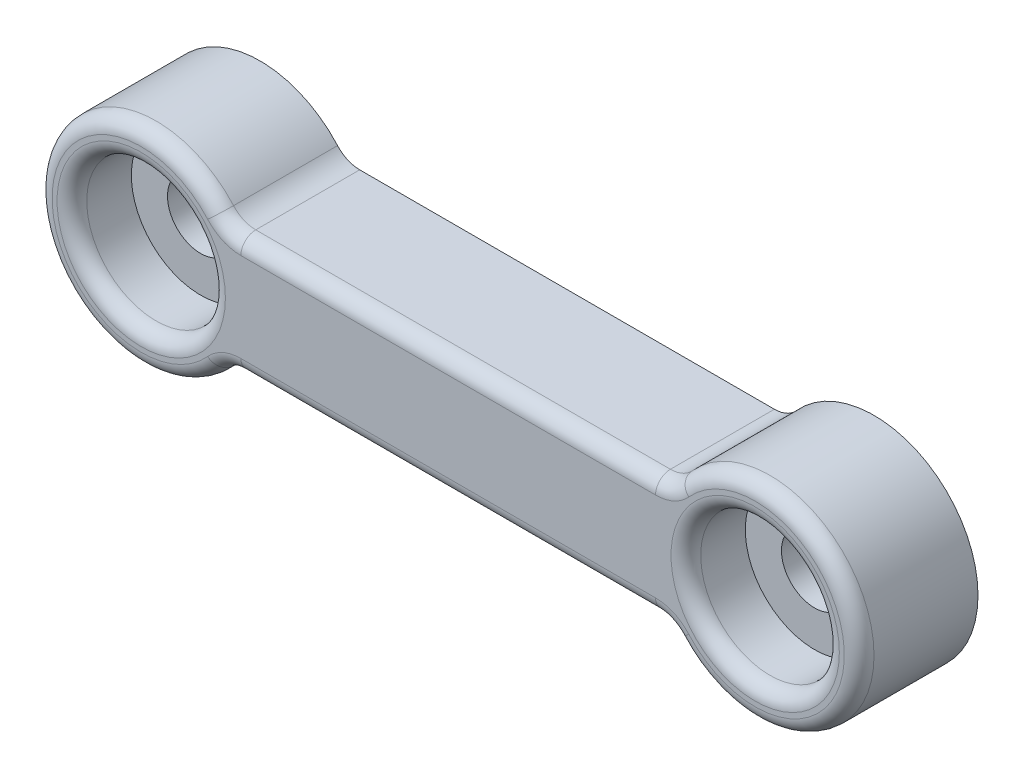
SolidWorks part; units mm, degrees
material "ABS"
ref_plane "Front Plane" through (0, 0, 0) normal (0, 0, 1) x (1, 0, 0)
ref_plane "Top Plane" through (0, 0, 0) normal (0, 1, 0) x (1, 0, 0)
ref_plane "Right Plane" through (0, 0, 0) normal (1, 0, 0) x (0, 0, -1)
sketch "Sketch1" plane through (0, 0, 0) normal (0, 0, 1) x (1, 0, 0)
  line L0 (-15.5, 0) -> (15.5, 0) construction
  line L1 (-10.4688, 3) -> (10.4688, 3)
  line L2 (-10.4688, -3) -> (10.4688, -3)
  circle A0 centre (15.5, 0) radius 1.675
  circle A1 centre (-15.5, 0) radius 1.675
  circle A2 centre (-15.5, 0) radius 3.25 construction
  circle A3 centre (15.5, 0) radius 3.25 construction
  arc A4 (11.5869, -3.5) -> (11.5869, 3.5) centre (15.5, 0) ccw
  arc A5 (-11.5869, 3.5) -> (-11.5869, -3.5) centre (-15.5, 0) ccw
  arc A6 (11.5869, -3.5) -> (10.4688, -3) centre (10.4688, -4.5) ccw
  arc A7 (11.5869, 3.5) -> (10.4688, 3) centre (10.4688, 4.5) cw
  arc A8 (-11.5869, -3.5) -> (-10.4688, -3) centre (-10.4688, -4.5) cw
  arc A9 (-11.5869, 3.5) -> (-10.4688, 3) centre (-10.4688, 4.5) ccw
  point P2 (0, 0)
  dimension "D2" = 3.35
  dimension "D3" = 6.5
  dimension "D4" = 10.5
  dimension "D7" = 1.5
  dimension "D1" = 31
  dimension "D5" = 6
  dimension "D6" = 3
extrude "Boss-Extrude1" add sketch "Sketch1" along normal blind 6
sketch "Sketch2" plane through (0, 0, 6) normal (0, 0, 1) x (1, 0, 0)
  circle A0 centre (-15.5, 0) radius 3.5
  circle A1 centre (15.5, 0) radius 3.5
  dimension "D1" = 7
extrude "Cut-Extrude1" cut sketch "Sketch2" against normal blind 3
fillet "Fillet1" radius 0.75 10 edges at (0, 3, 6) (11.0812, 3.1307, 6) (20.75, 0, 6) (11.0812, -3.1307, 6) (0, -3, 6) (-11.0812, -3.1307, 6) (-20.75, 0, 6) (19, 0, 6) (-12, 0, 6) (-11.0812, 3.1307, 6)
